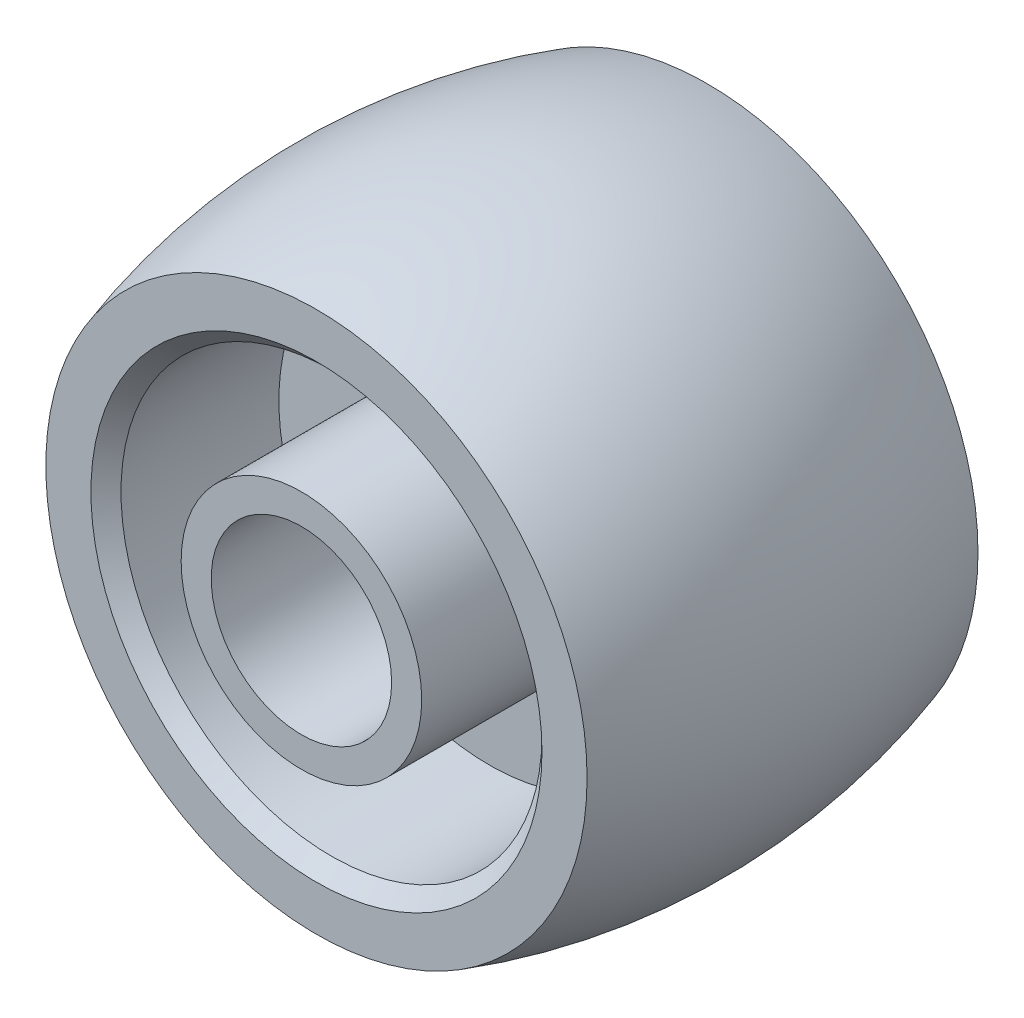
SolidWorks part; units mm, degrees
ref_plane "Plan de face" through (0, 0, 0) normal (0, 0, 1) x (1, 0, 0)
ref_plane "Plan de dessus" through (0, 0, 0) normal (0, 1, 0) x (1, 0, 0)
ref_plane "Plan de droite" through (0, 0, 0) normal (1, 0, 0) x (0, 0, -1)
sketch "Esquisse1" plane through (0, 0, 0) normal (1, 0, 0) x (0, 0, -1)
  line L0 (-4.7147, 0) -> (4.792, 0) construction
  line L1 (7, 3) -> (-7, 3)
  line L2 (-7, 3) -> (-7, 4)
  line L3 (-7, 4) -> (-0.75, 4)
  line L4 (-0.75, 4) -> (-0.75, 7)
  line L5 (-0.75, 7) -> (-6, 7)
  line L6 (-6.5, 7.5) -> (-6.5, 9)
  line L7 (0, -13.8929) -> (0, 13.236) construction
  line L8 (6.5, 7.5) -> (6.5, 9)
  line L9 (0.75, 7) -> (6, 7)
  line L10 (0.75, 4) -> (0.75, 7)
  line L11 (7, 4) -> (0.75, 4)
  line L12 (7, 3) -> (7, 4)
  line L13 (-6, 7) -> (-6.5, 7.5)
  line L14 (6, 7) -> (6.5, 7.5)
  arc A0 (6.5, 9) -> (-6.5, 9) centre (0, -11.625) ccw
  point P9 (-6.5, 7)
  point P13 (0, 3)
  point P14 (-0.75, 5.5)
  point P15 (0, -13.8929)
  point P16 (6.5, 7)
  point P22 (0, 3)
  point P26 (0, 10)
  dimension "D8" = 10
  dimension "D1" = 3
  dimension "D2" = 4
  dimension "D3" = 7
  dimension "D4" = 2
  dimension "D5" = 6.5
  dimension "D6" = 7
  dimension "D7" = 1.5
revolve "Révolution1" add sketch "Esquisse1" angle 360 about L0
